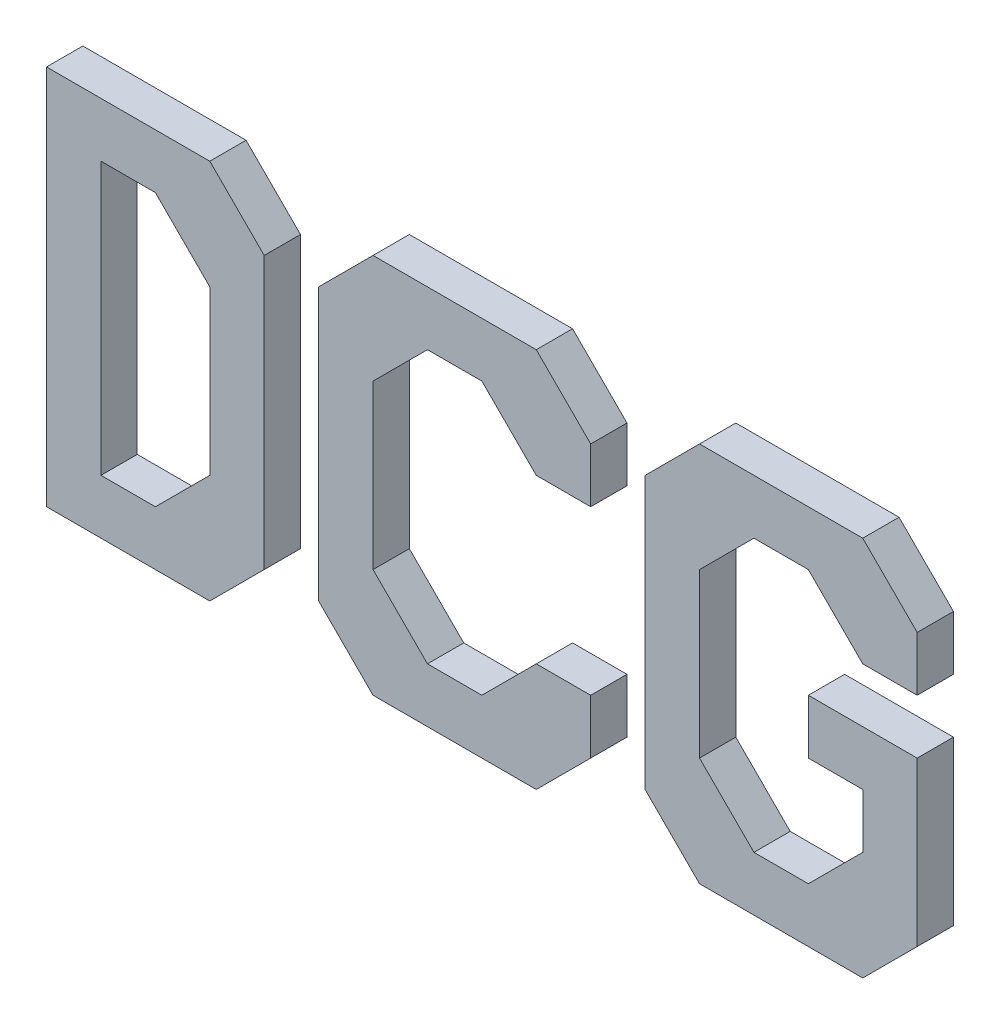
SolidWorks part; units mm, degrees
ref_plane "Front Plane" through (0, 0, 0) normal (0, 0, 1) x (1, 0, 0)
ref_plane "Top Plane" through (0, 0, 0) normal (0, 1, 0) x (1, 0, 0)
ref_plane "Right Plane" through (0, 0, 0) normal (1, 0, 0) x (0, 0, -1)
sketch "Sketch1" plane through (0, 0, 0) normal (0, 0, 1) x (1, 0, 0)
  line L0 (15, 15) -> (30, 15)
  line L1 (0, 0) -> (15, 0)
  line L2 (0, 0) -> (0, 15)
  line L3 (0, 15) -> (15, 15)
  line L4 (15, 0) -> (15, 15)
  line L5 (30, 0) -> (30, 15)
  line L6 (15, 0) -> (30, 0)
  line L7 (15, 0) -> (15, 15)
  line L8 (30, 15) -> (45, 15)
  line L9 (45, 0) -> (45, 15)
  line L10 (30, 0) -> (45, 0)
  line L11 (30, 0) -> (30, 15)
  line L12 (45, 15) -> (60, 15)
  line L13 (60, 0) -> (60, 15)
  line L14 (45, 0) -> (60, 0)
  line L15 (45, 0) -> (45, 15)
  line L16 (60, 15) -> (75, 15)
  line L17 (75, 0) -> (75, 15)
  line L18 (60, 0) -> (75, 0)
  line L19 (60, 0) -> (60, 15)
  line L20 (75, 15) -> (90, 15)
  line L21 (90, 0) -> (90, 15)
  line L22 (75, 0) -> (90, 0)
  line L23 (75, 0) -> (75, 15)
  line L24 (90, 15) -> (105, 15)
  line L25 (105, 0) -> (105, 15)
  line L26 (90, 0) -> (105, 0)
  line L27 (90, 0) -> (90, 15)
  line L28 (105, 15) -> (120, 15)
  line L29 (120, 0) -> (120, 15)
  line L30 (105, 0) -> (120, 0)
  line L31 (105, 0) -> (105, 15)
  line L32 (120, 15) -> (135, 15)
  line L33 (135, 0) -> (135, 15)
  line L34 (120, 0) -> (135, 0)
  line L35 (120, 0) -> (120, 15)
  line L36 (135, 15) -> (150, 15)
  line L37 (150, 0) -> (150, 15)
  line L38 (135, 0) -> (150, 0)
  line L39 (135, 0) -> (135, 15)
  line L40 (150, 15) -> (165, 15)
  line L41 (165, 0) -> (165, 15)
  line L42 (150, 0) -> (165, 0)
  line L43 (150, 0) -> (150, 15)
  line L44 (165, 15) -> (180, 15)
  line L45 (180, 0) -> (180, 15)
  line L46 (165, 0) -> (180, 0)
  line L47 (165, 0) -> (165, 15)
  line L48 (180, 15) -> (195, 15)
  line L49 (195, 0) -> (195, 15)
  line L50 (180, 0) -> (195, 0)
  line L51 (180, 0) -> (180, 15)
  line L52 (195, 15) -> (210, 15)
  line L53 (210, 0) -> (210, 15)
  line L54 (195, 0) -> (210, 0)
  line L55 (195, 0) -> (195, 15)
  line L56 (210, 15) -> (225, 15)
  line L57 (225, 0) -> (225, 15)
  line L58 (210, 0) -> (225, 0)
  line L59 (210, 0) -> (210, 15)
  line L60 (225, 15) -> (240, 15)
  line L61 (240, 0) -> (240, 15)
  line L62 (225, 0) -> (240, 0)
  line L63 (225, 0) -> (225, 15)
  line L64 (0, 30) -> (15, 30)
  line L65 (15, 15) -> (15, 30)
  line L66 (0, 15) -> (15, 15)
  line L67 (0, 15) -> (0, 30)
  line L68 (15, 30) -> (30, 30)
  line L69 (30, 15) -> (30, 30)
  line L70 (15, 15) -> (30, 15)
  line L71 (15, 15) -> (15, 30)
  line L72 (30, 30) -> (45, 30)
  line L73 (45, 15) -> (45, 30)
  line L74 (30, 15) -> (45, 15)
  line L75 (30, 15) -> (30, 30)
  line L76 (45, 30) -> (60, 30)
  line L77 (60, 15) -> (60, 30)
  line L78 (45, 15) -> (60, 15)
  line L79 (45, 15) -> (45, 30)
  line L80 (60, 30) -> (75, 30)
  line L81 (75, 15) -> (75, 30)
  line L82 (60, 15) -> (75, 15)
  line L83 (60, 15) -> (60, 30)
  line L84 (75, 30) -> (90, 30)
  line L85 (90, 15) -> (90, 30)
  line L86 (75, 15) -> (90, 15)
  line L87 (75, 15) -> (75, 30)
  line L88 (90, 30) -> (105, 30)
  line L89 (105, 15) -> (105, 30)
  line L90 (90, 15) -> (105, 15)
  line L91 (90, 15) -> (90, 30)
  line L92 (105, 30) -> (120, 30)
  line L93 (120, 15) -> (120, 30)
  line L94 (105, 15) -> (120, 15)
  line L95 (105, 15) -> (105, 30)
  line L96 (120, 30) -> (135, 30)
  line L97 (135, 15) -> (135, 30)
  line L98 (120, 15) -> (135, 15)
  line L99 (120, 15) -> (120, 30)
  line L100 (135, 30) -> (150, 30)
  line L101 (150, 15) -> (150, 30)
  line L102 (135, 15) -> (150, 15)
  line L103 (135, 15) -> (135, 30)
  line L104 (150, 30) -> (165, 30)
  line L105 (165, 15) -> (165, 30)
  line L106 (150, 15) -> (165, 15)
  line L107 (150, 15) -> (150, 30)
  line L108 (165, 30) -> (180, 30)
  line L109 (180, 15) -> (180, 30)
  line L110 (165, 15) -> (180, 15)
  line L111 (165, 15) -> (165, 30)
  line L112 (180, 30) -> (195, 30)
  line L113 (195, 15) -> (195, 30)
  line L114 (180, 15) -> (195, 15)
  line L115 (180, 15) -> (180, 30)
  line L116 (195, 30) -> (210, 30)
  line L117 (210, 15) -> (210, 30)
  line L118 (195, 15) -> (210, 15)
  line L119 (195, 15) -> (195, 30)
  line L120 (210, 30) -> (225, 30)
  line L121 (225, 15) -> (225, 30)
  line L122 (210, 15) -> (225, 15)
  line L123 (210, 15) -> (210, 30)
  line L124 (225, 30) -> (240, 30)
  line L125 (240, 15) -> (240, 30)
  line L126 (225, 15) -> (240, 15)
  line L127 (225, 15) -> (225, 30)
  line L128 (0, 45) -> (15, 45)
  line L129 (15, 30) -> (15, 45)
  line L130 (0, 30) -> (15, 30)
  line L131 (0, 30) -> (0, 45)
  line L132 (15, 45) -> (30, 45)
  line L133 (30, 30) -> (30, 45)
  line L134 (15, 30) -> (30, 30)
  line L135 (15, 30) -> (15, 45)
  line L136 (30, 45) -> (45, 45)
  line L137 (45, 30) -> (45, 45)
  line L138 (30, 30) -> (45, 30)
  line L139 (30, 30) -> (30, 45)
  line L140 (45, 45) -> (60, 45)
  line L141 (60, 30) -> (60, 45)
  line L142 (45, 30) -> (60, 30)
  line L143 (45, 30) -> (45, 45)
  line L144 (60, 45) -> (75, 45)
  line L145 (75, 30) -> (75, 45)
  line L146 (60, 30) -> (75, 30)
  line L147 (60, 30) -> (60, 45)
  line L148 (75, 45) -> (90, 45)
  line L149 (90, 30) -> (90, 45)
  line L150 (75, 30) -> (90, 30)
  line L151 (75, 30) -> (75, 45)
  line L152 (90, 45) -> (105, 45)
  line L153 (105, 30) -> (105, 45)
  line L154 (90, 30) -> (105, 30)
  line L155 (90, 30) -> (90, 45)
  line L156 (105, 45) -> (120, 45)
  line L157 (120, 30) -> (120, 45)
  line L158 (105, 30) -> (120, 30)
  line L159 (105, 30) -> (105, 45)
  line L160 (120, 45) -> (135, 45)
  line L161 (135, 30) -> (135, 45)
  line L162 (120, 30) -> (135, 30)
  line L163 (120, 30) -> (120, 45)
  line L164 (135, 45) -> (150, 45)
  line L165 (150, 30) -> (150, 45)
  line L166 (135, 30) -> (150, 30)
  line L167 (135, 30) -> (135, 45)
  line L168 (150, 45) -> (165, 45)
  line L169 (165, 30) -> (165, 45)
  line L170 (150, 30) -> (165, 30)
  line L171 (150, 30) -> (150, 45)
  line L172 (165, 45) -> (180, 45)
  line L173 (180, 30) -> (180, 45)
  line L174 (165, 30) -> (180, 30)
  line L175 (165, 30) -> (165, 45)
  line L176 (180, 45) -> (195, 45)
  line L177 (195, 30) -> (195, 45)
  line L178 (180, 30) -> (195, 30)
  line L179 (180, 30) -> (180, 45)
  line L180 (195, 45) -> (210, 45)
  line L181 (210, 30) -> (210, 45)
  line L182 (195, 30) -> (210, 30)
  line L183 (195, 30) -> (195, 45)
  line L184 (210, 45) -> (225, 45)
  line L185 (225, 30) -> (225, 45)
  line L186 (210, 30) -> (225, 30)
  line L187 (210, 30) -> (210, 45)
  line L188 (225, 45) -> (240, 45)
  line L189 (240, 30) -> (240, 45)
  line L190 (225, 30) -> (240, 30)
  line L191 (225, 30) -> (225, 45)
  line L192 (0, 60) -> (15, 60)
  line L193 (15, 45) -> (15, 60)
  line L194 (0, 45) -> (15, 45)
  line L195 (0, 45) -> (0, 60)
  line L196 (15, 60) -> (30, 60)
  line L197 (30, 45) -> (30, 60)
  line L198 (15, 45) -> (30, 45)
  line L199 (15, 45) -> (15, 60)
  line L200 (30, 60) -> (45, 60)
  line L201 (45, 45) -> (45, 60)
  line L202 (30, 45) -> (45, 45)
  line L203 (30, 45) -> (30, 60)
  line L204 (45, 60) -> (60, 60)
  line L205 (60, 45) -> (60, 60)
  line L206 (45, 45) -> (60, 45)
  line L207 (45, 45) -> (45, 60)
  line L208 (60, 60) -> (75, 60)
  line L209 (75, 45) -> (75, 60)
  line L210 (60, 45) -> (75, 45)
  line L211 (60, 45) -> (60, 60)
  line L212 (75, 60) -> (90, 60)
  line L213 (90, 45) -> (90, 60)
  line L214 (75, 45) -> (90, 45)
  line L215 (75, 45) -> (75, 60)
  line L216 (90, 60) -> (105, 60)
  line L217 (105, 45) -> (105, 60)
  line L218 (90, 45) -> (105, 45)
  line L219 (90, 45) -> (90, 60)
  line L220 (105, 60) -> (120, 60)
  line L221 (120, 45) -> (120, 60)
  line L222 (105, 45) -> (120, 45)
  line L223 (105, 45) -> (105, 60)
  line L224 (120, 60) -> (135, 60)
  line L225 (135, 45) -> (135, 60)
  line L226 (120, 45) -> (135, 45)
  line L227 (120, 45) -> (120, 60)
  line L228 (135, 60) -> (150, 60)
  line L229 (150, 45) -> (150, 60)
  line L230 (135, 45) -> (150, 45)
  line L231 (135, 45) -> (135, 60)
  line L232 (150, 60) -> (165, 60)
  line L233 (165, 45) -> (165, 60)
  line L234 (150, 45) -> (165, 45)
  line L235 (150, 45) -> (150, 60)
  line L236 (165, 60) -> (180, 60)
  line L237 (180, 45) -> (180, 60)
  line L238 (165, 45) -> (180, 45)
  line L239 (165, 45) -> (165, 60)
  line L240 (180, 60) -> (195, 60)
  line L241 (195, 45) -> (195, 60)
  line L242 (180, 45) -> (195, 45)
  line L243 (180, 45) -> (180, 60)
  line L244 (195, 60) -> (210, 60)
  line L245 (210, 45) -> (210, 60)
  line L246 (195, 45) -> (210, 45)
  line L247 (195, 45) -> (195, 60)
  line L248 (210, 60) -> (225, 60)
  line L249 (225, 45) -> (225, 60)
  line L250 (210, 45) -> (225, 45)
  line L251 (210, 45) -> (210, 60)
  line L252 (225, 60) -> (240, 60)
  line L253 (240, 45) -> (240, 60)
  line L254 (225, 45) -> (240, 45)
  line L255 (225, 45) -> (225, 60)
  line L256 (0, 75) -> (15, 75)
  line L257 (15, 60) -> (15, 75)
  line L258 (0, 60) -> (15, 60)
  line L259 (0, 60) -> (0, 75)
  line L260 (15, 75) -> (30, 75)
  line L261 (30, 60) -> (30, 75)
  line L262 (15, 60) -> (30, 60)
  line L263 (15, 60) -> (15, 75)
  line L264 (30, 75) -> (45, 75)
  line L265 (45, 60) -> (45, 75)
  line L266 (30, 60) -> (45, 60)
  line L267 (30, 60) -> (30, 75)
  line L268 (45, 75) -> (60, 75)
  line L269 (60, 60) -> (60, 75)
  line L270 (45, 60) -> (60, 60)
  line L271 (45, 60) -> (45, 75)
  line L272 (60, 75) -> (75, 75)
  line L273 (75, 60) -> (75, 75)
  line L274 (60, 60) -> (75, 60)
  line L275 (60, 60) -> (60, 75)
  line L276 (75, 75) -> (90, 75)
  line L277 (90, 60) -> (90, 75)
  line L278 (75, 60) -> (90, 60)
  line L279 (75, 60) -> (75, 75)
  line L280 (90, 75) -> (105, 75)
  line L281 (105, 60) -> (105, 75)
  line L282 (90, 60) -> (105, 60)
  line L283 (90, 60) -> (90, 75)
  line L284 (105, 75) -> (120, 75)
  line L285 (120, 60) -> (120, 75)
  line L286 (105, 60) -> (120, 60)
  line L287 (105, 60) -> (105, 75)
  line L288 (120, 75) -> (135, 75)
  line L289 (135, 60) -> (135, 75)
  line L290 (120, 60) -> (135, 60)
  line L291 (120, 60) -> (120, 75)
  line L292 (135, 75) -> (150, 75)
  line L293 (150, 60) -> (150, 75)
  line L294 (135, 60) -> (150, 60)
  line L295 (135, 60) -> (135, 75)
  line L296 (150, 75) -> (165, 75)
  line L297 (165, 60) -> (165, 75)
  line L298 (150, 60) -> (165, 60)
  line L299 (150, 60) -> (150, 75)
  line L300 (165, 75) -> (180, 75)
  line L301 (180, 60) -> (180, 75)
  line L302 (165, 60) -> (180, 60)
  line L303 (165, 60) -> (165, 75)
  line L304 (180, 75) -> (195, 75)
  line L305 (195, 60) -> (195, 75)
  line L306 (180, 60) -> (195, 60)
  line L307 (180, 60) -> (180, 75)
  line L308 (195, 75) -> (210, 75)
  line L309 (210, 60) -> (210, 75)
  line L310 (195, 60) -> (210, 60)
  line L311 (195, 60) -> (195, 75)
  line L312 (210, 75) -> (225, 75)
  line L313 (225, 60) -> (225, 75)
  line L314 (210, 60) -> (225, 60)
  line L315 (210, 60) -> (210, 75)
  line L316 (225, 75) -> (240, 75)
  line L317 (240, 60) -> (240, 75)
  line L318 (225, 60) -> (240, 60)
  line L319 (225, 60) -> (225, 75)
  line L320 (0, 90) -> (15, 90)
  line L321 (15, 75) -> (15, 90)
  line L322 (0, 75) -> (15, 75)
  line L323 (0, 75) -> (0, 90)
  line L324 (15, 90) -> (30, 90)
  line L325 (30, 75) -> (30, 90)
  line L326 (15, 75) -> (30, 75)
  line L327 (15, 75) -> (15, 90)
  line L328 (30, 90) -> (45, 90)
  line L329 (45, 75) -> (45, 90)
  line L330 (30, 75) -> (45, 75)
  line L331 (30, 75) -> (30, 90)
  line L332 (45, 90) -> (60, 90)
  line L333 (60, 75) -> (60, 90)
  line L334 (45, 75) -> (60, 75)
  line L335 (45, 75) -> (45, 90)
  line L336 (60, 90) -> (75, 90)
  line L337 (75, 75) -> (75, 90)
  line L338 (60, 75) -> (75, 75)
  line L339 (60, 75) -> (60, 90)
  line L340 (75, 90) -> (90, 90)
  line L341 (90, 75) -> (90, 90)
  line L342 (75, 75) -> (90, 75)
  line L343 (75, 75) -> (75, 90)
  line L344 (90, 90) -> (105, 90)
  line L345 (105, 75) -> (105, 90)
  line L346 (90, 75) -> (105, 75)
  line L347 (90, 75) -> (90, 90)
  line L348 (105, 90) -> (120, 90)
  line L349 (120, 75) -> (120, 90)
  line L350 (105, 75) -> (120, 75)
  line L351 (105, 75) -> (105, 90)
  line L352 (120, 90) -> (135, 90)
  line L353 (135, 75) -> (135, 90)
  line L354 (120, 75) -> (135, 75)
  line L355 (120, 75) -> (120, 90)
  line L356 (135, 90) -> (150, 90)
  line L357 (150, 75) -> (150, 90)
  line L358 (135, 75) -> (150, 75)
  line L359 (135, 75) -> (135, 90)
  line L360 (150, 90) -> (165, 90)
  line L361 (165, 75) -> (165, 90)
  line L362 (150, 75) -> (165, 75)
  line L363 (150, 75) -> (150, 90)
  line L364 (165, 90) -> (180, 90)
  line L365 (180, 75) -> (180, 90)
  line L366 (165, 75) -> (180, 75)
  line L367 (165, 75) -> (165, 90)
  line L368 (180, 90) -> (195, 90)
  line L369 (195, 75) -> (195, 90)
  line L370 (180, 75) -> (195, 75)
  line L371 (180, 75) -> (180, 90)
  line L372 (195, 90) -> (210, 90)
  line L373 (210, 75) -> (210, 90)
  line L374 (195, 75) -> (210, 75)
  line L375 (195, 75) -> (195, 90)
  line L376 (210, 90) -> (225, 90)
  line L377 (225, 75) -> (225, 90)
  line L378 (210, 75) -> (225, 75)
  line L379 (210, 75) -> (210, 90)
  line L380 (225, 90) -> (240, 90)
  line L381 (240, 75) -> (240, 90)
  line L382 (225, 75) -> (240, 75)
  line L383 (225, 75) -> (225, 90)
  line L384 (0, 105) -> (15, 105)
  line L385 (15, 90) -> (15, 105)
  line L386 (0, 90) -> (15, 90)
  line L387 (0, 90) -> (0, 105)
  line L388 (15, 105) -> (30, 105)
  line L389 (30, 90) -> (30, 105)
  line L390 (15, 90) -> (30, 90)
  line L391 (15, 90) -> (15, 105)
  line L392 (30, 105) -> (45, 105)
  line L393 (45, 90) -> (45, 105)
  line L394 (30, 90) -> (45, 90)
  line L395 (30, 90) -> (30, 105)
  line L396 (45, 105) -> (60, 105)
  line L397 (60, 90) -> (60, 105)
  line L398 (45, 90) -> (60, 90)
  line L399 (45, 90) -> (45, 105)
  line L400 (60, 105) -> (75, 105)
  line L401 (75, 90) -> (75, 105)
  line L402 (60, 90) -> (75, 90)
  line L403 (60, 90) -> (60, 105)
  line L404 (75, 105) -> (90, 105)
  line L405 (90, 90) -> (90, 105)
  line L406 (75, 90) -> (90, 90)
  line L407 (75, 90) -> (75, 105)
  line L408 (90, 105) -> (105, 105)
  line L409 (105, 90) -> (105, 105)
  line L410 (90, 90) -> (105, 90)
  line L411 (90, 90) -> (90, 105)
  line L412 (105, 105) -> (120, 105)
  line L413 (120, 90) -> (120, 105)
  line L414 (105, 90) -> (120, 90)
  line L415 (105, 90) -> (105, 105)
  line L416 (120, 105) -> (135, 105)
  line L417 (135, 90) -> (135, 105)
  line L418 (120, 90) -> (135, 90)
  line L419 (120, 90) -> (120, 105)
  line L420 (135, 105) -> (150, 105)
  line L421 (150, 90) -> (150, 105)
  line L422 (135, 90) -> (150, 90)
  line L423 (135, 90) -> (135, 105)
  line L424 (150, 105) -> (165, 105)
  line L425 (165, 90) -> (165, 105)
  line L426 (150, 90) -> (165, 90)
  line L427 (150, 90) -> (150, 105)
  line L428 (165, 105) -> (180, 105)
  line L429 (180, 90) -> (180, 105)
  line L430 (165, 90) -> (180, 90)
  line L431 (165, 90) -> (165, 105)
  line L432 (180, 105) -> (195, 105)
  line L433 (195, 90) -> (195, 105)
  line L434 (180, 90) -> (195, 90)
  line L435 (180, 90) -> (180, 105)
  line L436 (195, 105) -> (210, 105)
  line L437 (210, 90) -> (210, 105)
  line L438 (195, 90) -> (210, 90)
  line L439 (195, 90) -> (195, 105)
  line L440 (210, 105) -> (225, 105)
  line L441 (225, 90) -> (225, 105)
  line L442 (210, 90) -> (225, 90)
  line L443 (210, 90) -> (210, 105)
  line L444 (225, 105) -> (240, 105)
  line L445 (240, 90) -> (240, 105)
  line L446 (225, 90) -> (240, 90)
  line L447 (225, 90) -> (225, 105)
  dimension "D1" = 15
  dimension "D2" = 15
sketch "Sketch2" plane through (0, 0, 0) normal (0, 0, 1) x (1, 0, 0)
  line L0 (0, 0) -> (0, 105)
  line L1 (0, 105) -> (45, 105)
  line L2 (45, 105) -> (60, 90)
  line L3 (60, 90) -> (60, 15)
  line L4 (60, 15) -> (45, 0)
  line L5 (45, 0) -> (0, 0)
  line L6 (15, 90) -> (30, 90)
  line L7 (30, 90) -> (45, 75)
  line L8 (45, 75) -> (45, 30)
  line L9 (45, 30) -> (30, 15)
  line L10 (30, 15) -> (15, 15)
  line L11 (15, 15) -> (15, 90)
  line L12 (90, 0) -> (75, 15)
  line L13 (75, 15) -> (75, 90)
  line L14 (75, 90) -> (90, 105)
  line L15 (90, 105) -> (135, 105)
  line L16 (135, 105) -> (150, 90)
  line L17 (150, 90) -> (150, 75)
  line L18 (150, 75) -> (135, 75)
  line L19 (135, 75) -> (120, 90)
  line L20 (120, 90) -> (105, 90)
  line L21 (105, 90) -> (90, 75)
  line L22 (90, 75) -> (90, 30)
  line L23 (90, 30) -> (105, 15)
  line L24 (105, 15) -> (120, 15)
  line L25 (120, 15) -> (135, 30)
  line L26 (135, 30) -> (150, 30)
  line L27 (150, 30) -> (150, 15)
  line L28 (150, 15) -> (135, 0)
  line L29 (135, 0) -> (90, 0)
  line L30 (180, 0) -> (165, 15)
  line L31 (165, 15) -> (165, 90)
  line L32 (165, 90) -> (180, 105)
  line L33 (180, 105) -> (225, 105)
  line L34 (225, 105) -> (240, 90)
  line L35 (240, 90) -> (240, 75)
  line L36 (240, 75) -> (225, 75)
  line L37 (225, 75) -> (210, 90)
  line L38 (210, 90) -> (195, 90)
  line L39 (195, 90) -> (180, 75)
  line L40 (180, 75) -> (180, 30)
  line L41 (180, 30) -> (195, 15)
  line L42 (195, 15) -> (210, 15)
  line L43 (210, 15) -> (225, 30)
  line L44 (225, 30) -> (225, 45)
  line L45 (225, 45) -> (210, 45)
  line L46 (210, 45) -> (210, 60)
  line L47 (210, 60) -> (240, 60)
  line L48 (240, 60) -> (240, 15)
  line L49 (240, 15) -> (225, 0)
  line L50 (225, 0) -> (180, 0)
extrude "Extrude1" add sketch "Sketch2" along normal blind 10
